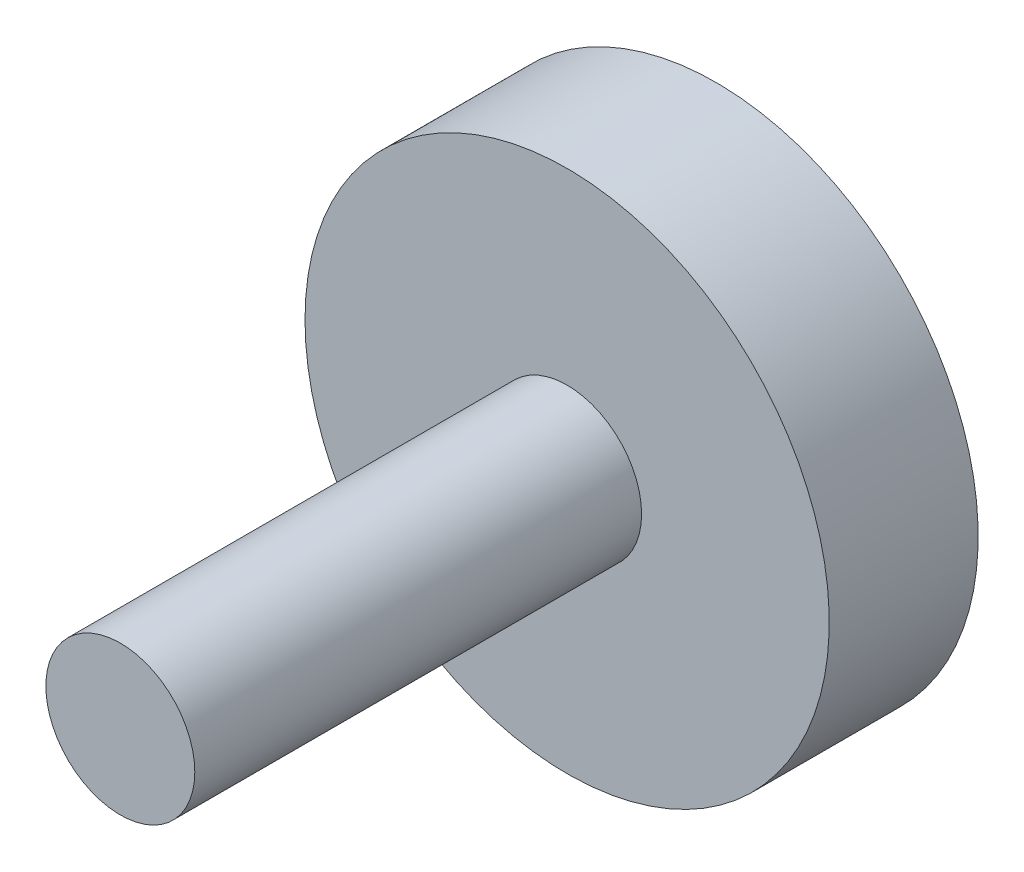
SolidWorks part; units mm, degrees
ref_plane "Front Plane" through (0, 0, 0) normal (0, 0, 1) x (1, 0, 0)
ref_plane "Top Plane" through (0, 0, 0) normal (0, 1, 0) x (1, 0, 0)
ref_plane "Right Plane" through (0, 0, 0) normal (1, 0, 0) x (0, 0, -1)
sketch "Sketch1" plane through (0, 0, 0) normal (0, 0, 1) x (1, 0, 0)
  circle A0 centre (0, 0) radius 5
  dimension "D1" = 10
extrude "Boss-Extrude1" add sketch "Sketch1" along normal blind 30 contours A0
ref_plane "Plane1" through (0, 0, 0) normal (0, 0, -1) x (-1, 0, 0)
sketch "Sketch2" plane through (0, 0, 0) normal (0, 0, -1) x (-1, 0, 0)
  circle A0 centre (0, 0) radius 17.6
  dimension "D1" = 35.2
extrude "Boss-Extrude2" add sketch "Sketch2" along normal blind 10
